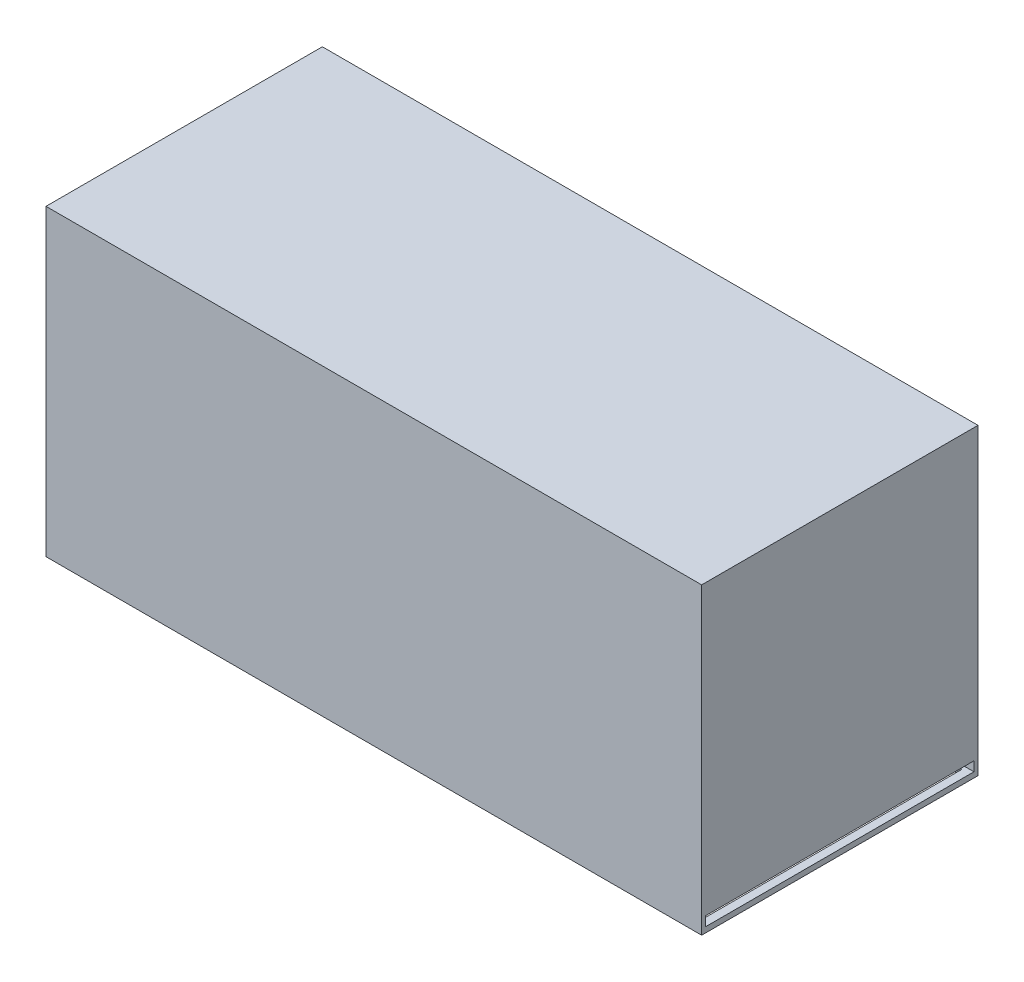
SolidWorks part; units mm, degrees
ref_plane "Piano frontale" through (0, 0, 0) normal (0, 0, 1) x (1, 0, 0)
ref_plane "Piano superiore" through (0, 0, 0) normal (0, 1, 0) x (1, 0, 0)
ref_plane "Piano destro" through (0, 0, 0) normal (1, 0, 0) x (0, 0, -1)
sketch "Schizzo1" plane through (0, 0, 0) normal (0, 0, 1) x (1, 0, 0)
  line L1 (0, 0) -> (121, 0)
  line L2 (0, 0) -> (0, 56)
  line L3 (0, 56) -> (121, 56)
  line L4 (121, 0) -> (121, 56)
  dimension "D1" = 121
  dimension "D2" = 56
extrude "Estrusione-Estrusione4" add sketch "Schizzo1" along normal blind 51
sketch "Schizzo6" plane through (0, 0, 0) normal (0, -1, 0) x (1, 0, 0)
  line L0 (0, 51) -> (121, 51) construction
  line L1 (1.5, 49.5) -> (119.5, 49.5)
  line L2 (1.5, 49.5) -> (1.5, 1.5)
  line L3 (1.5, 1.5) -> (119.5, 1.5)
  line L4 (119.5, 49.5) -> (119.5, 1.5)
  line L5 (0, 51) -> (0, 0) construction
  dimension "D1" = 48
  dimension "D2" = 118
  dimension "D3" = 1.5
  dimension "D4" = 1.5
extrude "Taglio-Estrusione2" cut sketch "Schizzo6" against normal blind 53
sketch "Schizzo7" plane through (0, 53, 0) normal (0, -1, 0) x (1, 0, 0)
  line L1 (1.5, 49.5) -> (23.5, 49.5)
  line L2 (1.5, 49.5) -> (1.5, 21.5)
  line L3 (1.5, 21.5) -> (23.5, 21.5)
  line L4 (23.5, 49.5) -> (23.5, 21.5)
  dimension "D1" = 22
  dimension "D2" = 28
extrude "Estrusione-Estrusione5" add sketch "Schizzo7" along normal blind 48
sketch "Schizzo13" plane through (0, 5, 0) normal (0, -1, 0) x (1, 0, 0)
  line L0 (23.5, 21.5) -> (23.5, 49.5) construction
  line L1 (2.5, 48.5) -> (22.5, 48.5)
  line L2 (2.5, 48.5) -> (2.5, 22.5)
  line L3 (2.5, 22.5) -> (22.5, 22.5)
  line L4 (22.5, 48.5) -> (22.5, 22.5)
  line L5 (1.5, 21.5) -> (23.5, 21.5) construction
  dimension "D1" = 26
  dimension "D2" = 20
  dimension "D3" = 1
  dimension "D4" = 1
extrude "Taglio-Estrusione3" cut sketch "Schizzo13" against normal blind 48
sketch "Schizzo15" plane through (0, 53, 0) normal (0, -1, 0) x (1, 0, 0)
  line L0 (1.5, 21.5) -> (1.5, 1.5) construction
  line L1 (1.5, 6.5) -> (119.5, 6.5)
  line L2 (1.5, 6.5) -> (1.5, 7.5)
  line L3 (1.5, 7.5) -> (119.5, 7.5)
  line L4 (119.5, 6.5) -> (119.5, 7.5)
  line L5 (119.5, 1.5) -> (119.5, 49.5) construction
  line L6 (1.5, 1.5) -> (119.5, 1.5) construction
  dimension "D1" = 1
  dimension "D2" = 5
extrude "Estrusione-Estrusione6" add sketch "Schizzo15" along normal blind 2
sketch "Schizzo16" plane through (0, 51, 0) normal (0, -1, 0) x (1, 0, 0)
  line L0 (119.5, 7.5) -> (1.5, 7.5) construction
  line L1 (116.5, 7.5) -> (119.5, 7.5)
  line L2 (116.5, 7.5) -> (116.5, 6.5)
  line L3 (116.5, 6.5) -> (119.5, 6.5)
  line L4 (119.5, 7.5) -> (119.5, 6.5)
  line L5 (119.5, 1.5) -> (119.5, 6.5) construction
  line L6 (119.5, 1.5) -> (119.5, 49.5) construction
  dimension "D1" = 3
extrude "Estrusione-Estrusione7" add sketch "Schizzo16" along normal blind 48
sketch "Schizzo17" plane through (121, 0, 0) normal (1, 0, 0) x (0, 0, -1)
  line L0 (-51, 0) -> (-51, 56) construction
  line L1 (-50.25, 2.75) -> (-0.75, 2.75)
  line L2 (-50.25, 2.75) -> (-50.25, 1)
  line L3 (-50.25, 1) -> (-0.75, 1)
  line L4 (-0.75, 2.75) -> (-0.75, 1)
  line L5 (0, 0) -> (0, 56) construction
  line L6 (-51, 0) -> (0, 0) construction
  dimension "D1" = 0.75
  dimension "D2" = 0.75
  dimension "D3" = 1
  dimension "D4" = 1.75
extrude "Taglio-Estrusione4" cut sketch "Schizzo17" against normal blind 120
